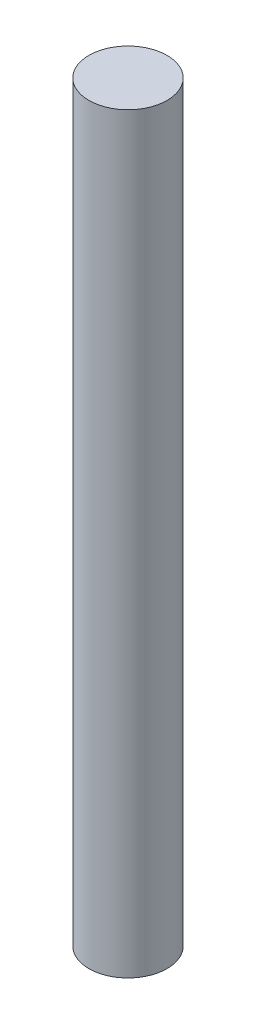
SolidWorks part; units mm, degrees
ref_plane "Front Plane" through (0, 0, 0) normal (0, 0, 1) x (1, 0, 0)
ref_plane "Top Plane" through (0, 0, 0) normal (0, 1, 0) x (1, 0, 0)
ref_plane "Right Plane" through (0, 0, 0) normal (1, 0, 0) x (0, 0, -1)
sketch "Croquis1" plane through (0, 0, 0) normal (0, 1, 0) x (1, 0, 0)
  circle A0 centre (0, 0) radius 4
  dimension "D1" = 8
extrude "Saliente-Extruir1" add sketch "Croquis1" along normal blind 77
